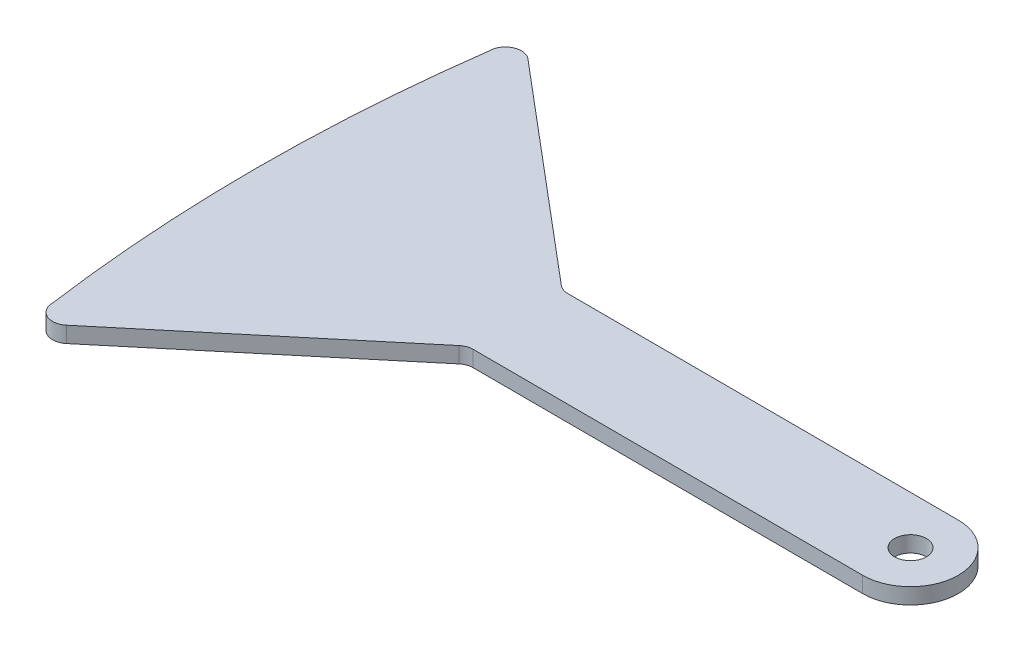
SolidWorks part; units mm, degrees
ref_plane "Front Plane" through (0, 0, 0) normal (0, 0, 1) x (1, 0, 0)
ref_plane "Top Plane" through (0, 0, 0) normal (0, 1, 0) x (1, 0, 0)
ref_plane "Right Plane" through (0, 0, 0) normal (1, 0, 0) x (0, 0, -1)
sketch "Sketch1" plane through (0, 0, 0) normal (0, 1, 0) x (1, 0, 0)
  line L0 (0, 0) -> (25, 0) construction
  line L1 (0.4359, 3.0567) -> (25.0069, 3)
  line L2 (0.4953, -2.9434) -> (24.9931, -3)
  line L3 (-0.2063, 3.2922) -> (-13.5746, 14.5622)
  line L5 (-13.5782, -14.3924) -> (-0.148, -3.1759)
  arc A1 (24.9931, -3) -> (25.0069, 3) centre (25, 0) ccw
  arc A2 (-15.2192, -13.6249) -> (-13.5782, -14.3924) centre (-14.2192, -13.6249) ccw
  arc A3 (-13.5746, 14.5622) -> (-15.2192, 13.7977) centre (-14.2192, 13.7977) ccw
  arc A4 (0.4953, -2.9434) -> (-0.148, -3.1759) centre (0.493, -3.9434) ccw
  arc A5 (0.4359, 3.0567) -> (-0.2063, 3.2922) centre (0.4383, 4.0567) cw
  arc A6 (-15.2192, 13.7977) -> (-15.2192, -13.6249) centre (84.6552, 0.0864) ccw
  circle A7 centre (25, 0) radius 1
  point P3 (12.5, 0)
  point P12 (-15.2192, -15.7629)
  point P15 (-15.2192, 15.9487)
  point P18 (0.1314, -2.9426)
  point P21 (0.072, 3.0576)
  dimension "D7" = 1
  dimension "D8" = 2
  dimension "D1" = 6
  dimension "D2" = 25
  dimension "D3" = 20
  dimension "D4" = 20
  dimension "D5" = 140
  dimension "D6" = 140
extrude "Boss-Extrude3" add sketch "Sketch1" along normal blind 1
sketch "Sketch3" plane through (0, 0, 0) normal (0, -1, 0) x (1, 0, 0)
  circle A0 centre (0, 0) radius 1
  dimension "D1" = 2
extrude "Boss-Extrude4" add sketch "Sketch3" along normal blind 1
